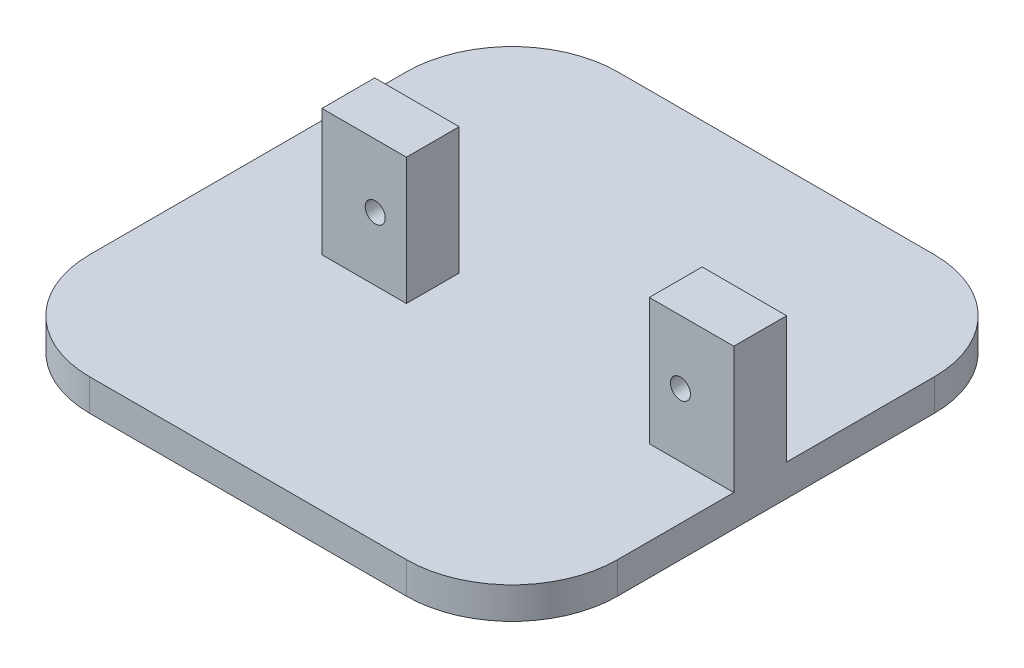
SolidWorks part; units mm, degrees
ref_plane "前视基准面" through (0, 0, 0) normal (0, 0, 1) x (1, 0, 0)
ref_plane "上视基准面" through (0, 0, 0) normal (0, 1, 0) x (1, 0, 0)
ref_plane "右视基准面" through (0, 0, 0) normal (1, 0, 0) x (0, 0, -1)
sketch "草图1" plane through (0, 0, 0) normal (0, 1, 0) x (1, 0, 0)
  line L1 (-15, 25) -> (15, 25)
  line L2 (-25, 15) -> (-25, -15)
  line L3 (-15, -25) -> (15, -25)
  line L4 (25, 15) -> (25, -15)
  line L5 (-25, 25) -> (25, -25) construction
  line L6 (-25, -25) -> (25, 25) construction
  arc A0 (25, -15) -> (15, -25) centre (15, -15) cw
  arc A1 (-15, -25) -> (-25, -15) centre (-15, -15) cw
  arc A2 (25, 15) -> (15, 25) centre (15, 15) ccw
  arc A3 (-15, 25) -> (-25, 15) centre (-15, 15) ccw
  point P0 (0, 0)
  dimension "D3" = 10
  dimension "D1" = 50
  dimension "D2" = 50
extrude "凸台-拉伸1" add sketch "草图1" along normal blind 3 contours A3 L2 A1 L3 A0 L4 A2 L1
sketch "草图2" plane through (0, 0, 0) normal (0, 1, 0) x (1, 0, 0)
  line L0 (-15, -25) -> (15, -25) construction
  line L1 (-7, 16.2) -> (25, 16.2) construction
  line L2 (-7, 16.2) -> (-7, -19) construction
  line L3 (-7, -19) -> (25, -19) construction
  line L4 (25, 16.2) -> (25, -19) construction
  line L5 (25, 15) -> (25, -15) construction
  line L6 (17, 1) -> (-6, 1) construction
  line L7 (17, 1) -> (25, 1)
  line L8 (17, 1) -> (17, -4)
  line L9 (17, -4) -> (25, -4)
  line L10 (25, 1) -> (25, -4)
  line L12 (-6, 1) -> (-14, 1)
  line L13 (-6, 1) -> (-6, -4)
  line L14 (-6, -4) -> (-14, -4)
  line L15 (-14, 1) -> (-14, -4)
  dimension "D1" = 35.2
  dimension "D2" = 32
  dimension "D3" = 6
  dimension "D4" = 0
  dimension "D5" = 5
  dimension "D6" = 20
  dimension "D7" = 8
  dimension "D8" = 0
  dimension "D9" = 23
  dimension "D10" = 8
extrude "凸台-拉伸2" add sketch "草图2" along normal blind 15
ref_plane "基准面1" through (0, 0, -1) normal (0, 0, -1) x (-1, 0, 0)
sketch "草图3" plane through (0, 0, -1) normal (0, 0, -1) x (-1, 0, 0)
  line L0 (6, 15) -> (6, 3) construction
  line L4 (14, 3) -> (6, 3) construction
  line L8 (-17, 3) -> (-25, 3) construction
  circle A0 centre (8.95, 9) radius 0.95
  circle A1 centre (-19.95, 9) radius 0.95
  point P13 (-19.3424, 3)
  dimension "D2" = 1.9
  dimension "D4" = 1.9
  dimension "D1" = 2.95
  dimension "D3" = 6
  dimension "D5" = 6
extrude "切除-拉伸1" cut sketch "草图3" against normal blind 15
